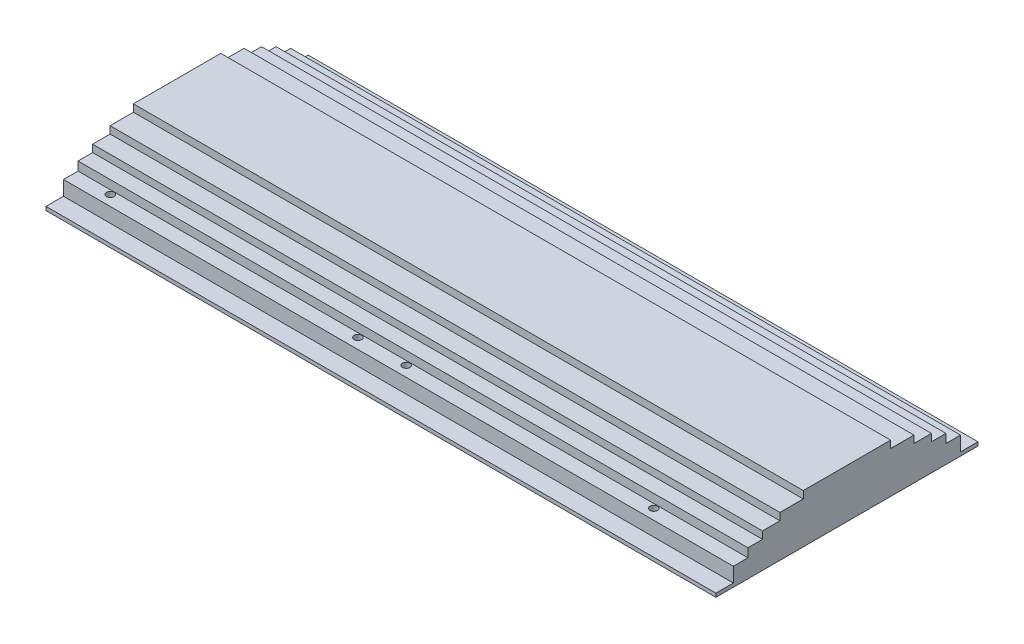
SolidWorks part; units mm, degrees
material "Rubber"
ref_plane "Front Plane" through (0, 0, 0) normal (0, 0, 1) x (1, 0, 0)
ref_plane "Top Plane" through (0, 0, 0) normal (0, 1, 0) x (1, 0, 0)
ref_plane "Right Plane" through (0, 0, 0) normal (1, 0, 0) x (0, 0, -1)
sketch "Sketch1" plane through (0, 0, 0) normal (0, 1, 0) x (1, 0, 0)
  line L1 (-127, 57.15) -> (165.1, 57.15)
  line L2 (-127, 57.15) -> (-127, -57.15)
  line L3 (-127, -57.15) -> (165.1, -57.15)
  line L4 (165.1, 57.15) -> (165.1, -57.15)
  dimension "D1" = 292.1
  dimension "D2" = 114.3
  dimension "D3" = 57.15
  dimension "D4" = 127
extrude "Extrude1" add sketch "Sketch1" along normal blind 1.6002
sketch "Sketch3" plane through (0, 1.6002, 0) normal (0, 1, 0) x (-1, 0, 0)
  line L0 (-165.1, 57.15) -> (-165.1, -57.15) construction
  line L1 (-165.1, -49.53) -> (127, -49.53)
  line L2 (-165.1, -49.53) -> (-165.1, 49.53)
  line L3 (-165.1, 49.53) -> (127, 49.53)
  line L4 (127, -49.53) -> (127, 49.53)
  line L5 (127, -57.15) -> (127, 57.15) construction
  line L6 (-165.1, -57.15) -> (127, -57.15) construction
  line L7 (127, 57.15) -> (-165.1, 57.15) construction
  dimension "D1" = 7.62
  dimension "D2" = 7.62
extrude "Extrude2" add sketch "Sketch3" along normal blind 6.35
hole_wizard "#4 Clearance Hole1" positions "3DSketch1" profile "Sketch2" hole size "#4" standard "Ansi Inch"
sketch3d "3DSketch1"
  line L0 (-127, 1.6002, -57.15) -> (-127, 1.6002, -49.53) construction
  line L1 (165.1, 1.6002, -57.15) -> (-127, 1.6002, -57.15) construction
  point P0 (125.8773, 1.6002, 44.9986)
  point P2 (17.8765, 1.6002, 44.9986)
  point P4 (17.8765, 1.6002, -45.0012)
  point P6 (125.8773, 1.6002, -45.0012)
  point P8 (-111.125, 1.6002, -45.0012)
  point P10 (-3.1242, 1.6002, -45.0012)
  point P12 (-3.1242, 1.6002, 44.9986)
  point P14 (-111.125, 1.6002, 44.9986)
  dimension "D1" = 15.875
  dimension "D2" = 89.9998
  dimension "D3" = 108.0008
  dimension "D4" = 108.0008
  dimension "D5" = 12.1488
  dimension "D6" = 21.0007
sketch "Sketch2" plane through (125.8773, 1.6002, 44.9986) normal (1, 0, 0) x (0, 0, 1)
  line L0 (0, 0) -> (0, 26.3806)
  line L1 (0, 26.3806) -> (1.6319, 25.4)
  line L2 (1.6319, 25.4) -> (1.6319, 0)
  line L5 (1.6319, 0) -> (0, 0)
  line L10 (0, 26.3806) -> (-1.632, 25.4) construction
  line L11 (0, -6.35) -> (0, 107.95) construction
  dimension "Hole Dia." = 3.2639
  dimension "Hole Depth" = 25.4
  dimension "Drill Angle" = 118
sketch "Sketch4" plane through (0, 7.9502, 0) normal (0, 1, 0) x (-1, 0, 0)
  line L0 (-165.1, 49.53) -> (-165.1, -49.53) construction
  line L1 (-165.1, -43.18) -> (127, -43.18)
  line L2 (-165.1, -43.18) -> (-165.1, 43.18)
  line L3 (-165.1, 43.18) -> (127, 43.18)
  line L4 (127, -43.18) -> (127, 43.18)
  line L5 (127, -49.53) -> (127, 49.53) construction
  line L6 (-165.1, -49.53) -> (127, -49.53) construction
  line L7 (127, 49.53) -> (-165.1, 49.53) construction
  dimension "D1" = 6.35
  dimension "D2" = 6.35
extrude "Extrude3" add sketch "Sketch4" along normal blind 3.81
sketch "Sketch5" plane through (0, 11.7602, 0) normal (0, 1, 0) x (-1, 0, 0)
  line L0 (127, -43.18) -> (127, 43.18) construction
  line L1 (127, -36.83) -> (-165.1, -36.83)
  line L2 (127, -36.83) -> (127, 36.83)
  line L3 (127, 36.83) -> (-165.1, 36.83)
  line L4 (-165.1, -36.83) -> (-165.1, 36.83)
  line L5 (-165.1, 43.18) -> (-165.1, -43.18) construction
  line L6 (-165.1, -43.18) -> (127, -43.18) construction
  line L7 (127, 43.18) -> (-165.1, 43.18) construction
  dimension "D1" = 6.35
  dimension "D2" = 6.35
extrude "Extrude4" add sketch "Sketch5" along normal blind 3.175
sketch "Sketch6" plane through (0, 14.9352, 0) normal (0, 1, 0) x (-1, 0, 0)
  line L0 (127, -36.83) -> (127, 36.83) construction
  line L1 (127, -29.21) -> (-165.1, -29.21)
  line L2 (127, -29.21) -> (127, 29.21)
  line L3 (127, 29.21) -> (-165.1, 29.21)
  line L4 (-165.1, -29.21) -> (-165.1, 29.21)
  line L5 (-165.1, 36.83) -> (-165.1, -36.83) construction
  line L6 (-165.1, -36.83) -> (127, -36.83) construction
  line L7 (127, 36.83) -> (-165.1, 36.83) construction
  dimension "D1" = 7.62
  dimension "D2" = 7.62
extrude "Extrude5" add sketch "Sketch6" along normal blind 3.175
sketch "Sketch7" plane through (0, 18.1102, 0) normal (0, 1, 0) x (-1, 0, 0)
  line L0 (127, -29.21) -> (127, 29.21) construction
  line L1 (127, -19.05) -> (-165.1, -19.05)
  line L2 (127, -19.05) -> (127, 19.05)
  line L3 (127, 19.05) -> (-165.1, 19.05)
  line L4 (-165.1, -19.05) -> (-165.1, 19.05)
  line L5 (-165.1, 29.21) -> (-165.1, -29.21) construction
  line L6 (-165.1, -29.21) -> (127, -29.21) construction
  line L7 (127, 29.21) -> (-165.1, 29.21) construction
  dimension "D1" = 10.16
  dimension "D2" = 10.16
extrude "Extrude6" add sketch "Sketch7" along normal blind 3.175
sketch "Sketch8" plane through (0, 0, 0) normal (0, -1, 0) x (1, 0, 0)
  line L0 (165.1, 0) -> (-127, 0) construction
  line L1 (165.1, 57.15) -> (165.1, -57.15) construction
  line L2 (-127, -57.15) -> (-127, 57.15) construction
  line L3 (17.8765, 44.9986) -> (-3.1242, 44.9986) construction
  line L6 (17.8765, -45.0012) -> (-3.1242, -45.0012) construction
  line L7 (7.3762, 44.9986) -> (7.3762, -45.0012) construction
  circle A0 centre (125.8773, -45.0012) radius 1.632
  circle A1 centre (17.8765, -45.0012) radius 1.6319
  circle A2 centre (125.8773, -45.0012) radius 1.6319 construction
  circle A3 centre (17.8765, -45.0012) radius 1.6319 construction
  circle A4 centre (-3.1242, 44.9986) radius 1.6319 construction
  circle A5 centre (-3.1242, -45.0012) radius 1.6319
  circle A6 centre (-111.125, -45.0012) radius 1.632
  circle A7 centre (-111.125, 45.0012) radius 1.632
  circle A8 centre (-3.1242, 45.0012) radius 1.6319
  circle A9 centre (17.8765, 45.0012) radius 1.6319
  circle A10 centre (125.8773, 45.0012) radius 1.632
extrude "Cut-Extrude1" cut sketch "Sketch8" against normal through all
